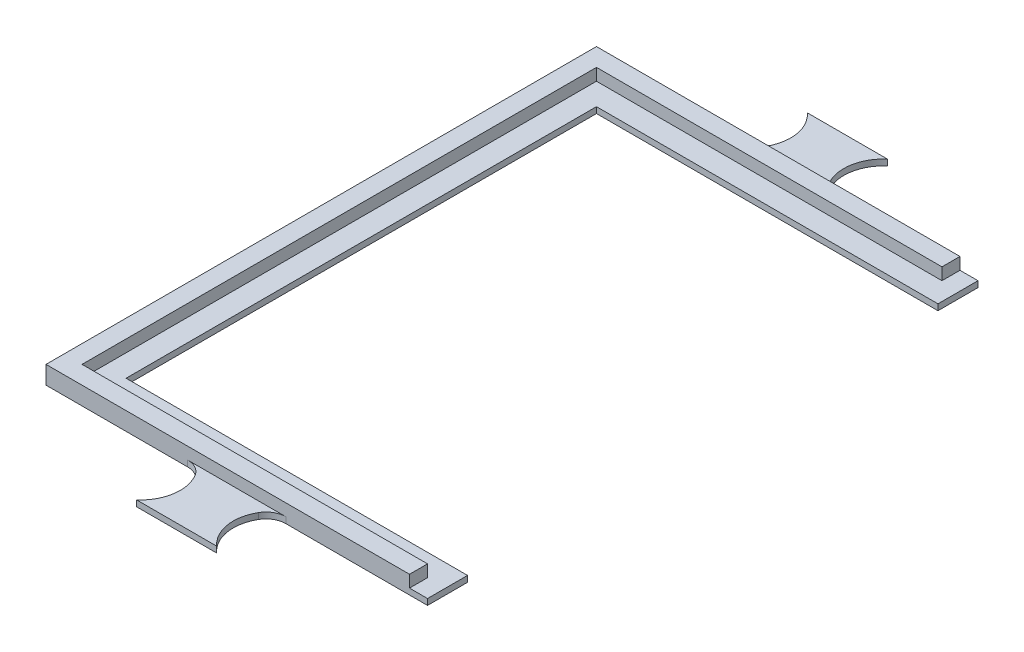
SolidWorks part; units mm, degrees
ref_plane "Front Plane" through (0, 0, 0) normal (0, 0, 1) x (1, 0, 0)
ref_plane "Top Plane" through (0, 0, 0) normal (0, 1, 0) x (1, 0, 0)
ref_plane "Right Plane" through (0, 0, 0) normal (1, 0, 0) x (0, 0, -1)
sketch "Sketch1" plane through (0, 0, 0) normal (0, 1, 0) x (1, 0, 0)
  line L1 (-42.65, -63.75) -> (42.65, -63.75) construction
  line L2 (-42.65, -63.75) -> (-42.65, 63.75) construction
  line L3 (-42.65, 63.75) -> (42.65, 63.75) construction
  line L4 (42.65, -63.75) -> (42.65, 63.75) construction
  line L5 (0, 63.75) -> (0, -63.75) construction
  line L6 (-42.65, 0) -> (42.65, 0) construction
  line L11 (-10, -83.75) -> (10, -83.75)
  line L12 (-47.65, -68.75) -> (-12.2843, -68.75)
  line L14 (-47.65, -68.75) -> (-47.65, -58.75)
  line L15 (-47.65, -58.75) -> (47.65, -58.75)
  line L16 (47.65, -68.75) -> (47.65, -58.75)
  line L17 (0, -58.75) -> (0, -68.75) construction
  line L18 (-47.65, -63.75) -> (47.65, -63.75) construction
  line L19 (12.2843, -68.75) -> (47.65, -68.75)
  line L20 (-47.65, 63.75) -> (47.65, 63.75) construction
  line L21 (0, 58.75) -> (0, 68.75) construction
  line L22 (-42.65, 63.75) -> (42.65, 63.75) construction
  line L23 (12.2843, 68.75) -> (47.65, 68.75)
  line L24 (47.65, 68.75) -> (47.65, 58.75)
  line L25 (-47.65, 58.75) -> (47.65, 58.75)
  line L26 (-47.65, 68.75) -> (-47.65, 58.75)
  line L27 (-47.65, 68.75) -> (-12.2843, 68.75)
  line L28 (-10, 83.75) -> (10, 83.75)
  line L30 (-37.65, -58.75) -> (-47.65, -58.75)
  line L31 (-37.65, -58.75) -> (-37.65, 58.75)
  line L32 (-37.65, 58.75) -> (-47.65, 58.75)
  line L33 (-47.65, -58.75) -> (-47.65, 58.75)
  line L34 (-42.65, 58.75) -> (-42.65, -58.75) construction
  line L35 (-37.65, 0) -> (-47.65, 0) construction
  arc A4 (-7.9541, -71.25) -> (-10, -83.75) centre (-16.6144, -76.25) cw
  arc A5 (7.9541, -71.25) -> (10, -83.75) centre (16.6144, -76.25) ccw
  arc A6 (7.9541, -71.25) -> (12.2843, -68.75) centre (12.2843, -73.75) cw
  arc A7 (-7.9541, -71.25) -> (-12.2843, -68.75) centre (-12.2843, -73.75) ccw
  arc A8 (-7.9541, 71.25) -> (-12.2843, 68.75) centre (-12.2843, 73.75) cw
  arc A9 (7.9541, 71.25) -> (12.2843, 68.75) centre (12.2843, 73.75) ccw
  arc A10 (7.9541, 71.25) -> (10, 83.75) centre (16.6144, 76.25) cw
  arc A11 (-7.9541, 71.25) -> (-10, 83.75) centre (-16.6144, 76.25) ccw
  point P0 (0, 0)
  point P15 (10, -68.75)
  point P18 (-10, -68.75)
  point P37 (-10, 68.75)
  point P38 (10, 68.75)
  dimension "D5" = 10
  dimension "D7" = 15
  dimension "D8" = 5
  dimension "D1" = 127.5
  dimension "D2" = 85.3
  dimension "D3" = 5
  dimension "D4" = 5
  dimension "D6" = 10
extrude "Boss-Extrude1" add sketch "Sketch1" along normal blind 1.5 contours A7 A4 L11 A5 A6 L19 L16 L15 L14 L12 | L33 L15 L31 L25 | A11 A8 L27 L26 L25 L24 L23 A9 A10 L28
sketch "Sketch2" plane through (0, 1.5, 0) normal (0, 1, 0) x (1, 0, 0)
  line L0 (43.15, 64.25) -> (43.15, 68.75)
  line L1 (-42.65, -63.75) -> (42.65, -63.75) construction
  line L2 (-42.65, -63.75) -> (-42.65, 63.75) construction
  line L3 (-42.65, 63.75) -> (42.65, 63.75) construction
  line L4 (42.65, -63.75) -> (42.65, 63.75) construction
  line L5 (0, 63.75) -> (0, -63.75) construction
  line L6 (-42.65, 0) -> (42.65, 0) construction
  line L7 (47.65, -68.75) -> (-47.65, -68.75)
  line L8 (47.65, -68.75) -> (47.65, 68.75)
  line L9 (47.65, 68.75) -> (-47.65, 68.75)
  line L10 (-47.65, -68.75) -> (-47.65, 68.75)
  line L11 (0, 68.75) -> (0, -68.75) construction
  line L12 (47.65, 0) -> (-47.65, 0) construction
  line L13 (43.15, -64.25) -> (-43.15, -64.25)
  line L14 (43.15, -64.25) -> (43.15, 64.25)
  line L15 (43.15, 64.25) -> (-43.15, 64.25)
  line L16 (-43.15, -64.25) -> (-43.15, 64.25)
  line L17 (0, 64.25) -> (0, -64.25) construction
  line L18 (43.15, 0) -> (-43.15, 0) construction
  line L19 (43.15, -64.25) -> (43.15, -68.75)
  point P0 (0, 0)
  point P4 (0, 0)
  point P8 (0, 0)
  line M8 (12.2843, -68.75) -> (47.65, -68.75)
  line M14 (47.65, 68.75) -> (12.2843, 68.75)
  line M20 (-12.2843, 68.75) -> (-47.65, 68.75)
  line M21 (-47.65, 68.75) -> (-47.65, -68.75)
  line M22 (-47.65, -68.75) -> (-12.2843, -68.75)
  dimension "D1" = 127.5
  dimension "D2" = 85.3
  dimension "D3" = 0.5
  dimension "D4" = 0.5
extrude "Boss-Extrude2" add sketch "Sketch2" along normal blind 3 contours L19 L13 L16 L15 L0 L9 L7 M14 M20 M21 M22 M8
